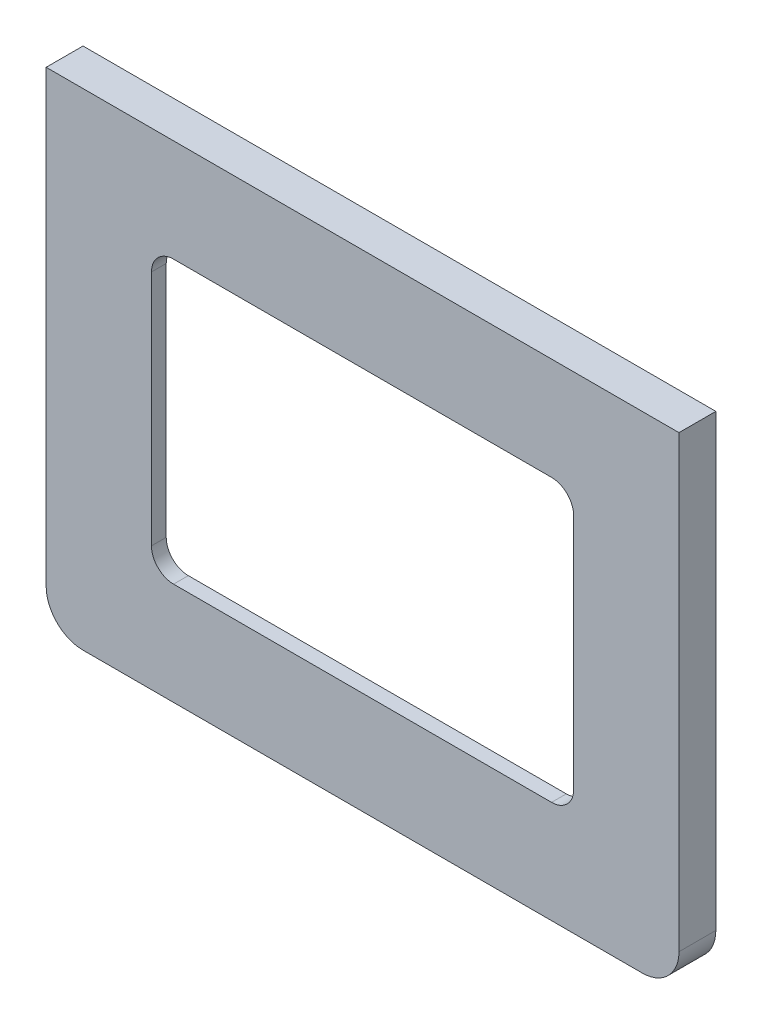
SolidWorks part; units mm, degrees
material "1023 Carbon Steel Sheet (SS)"
ref_plane "Front Plane" through (0, 0, 0) normal (0, 0, 1) x (1, 0, 0)
ref_plane "Top Plane" through (0, 0, 0) normal (0, 1, 0) x (1, 0, 0)
ref_plane "Right Plane" through (0, 0, 0) normal (1, 0, 0) x (0, 0, -1)
sketch "Sketch1" plane through (0, 0, 0) normal (0, 0, 1) x (1, 0, 0)
  line L0 (0, 30) -> (79.87, 30) construction
  line L1 (0, 0) -> (79.87, 0)
  line L2 (0, 0) -> (0, 60)
  line L3 (0, 60) -> (79.87, 60)
  line L4 (79.87, 0) -> (79.87, 60)
  line L5 (11.29, 10.905) -> (68.58, 10.905)
  line L6 (11.29, 10.905) -> (11.29, 49.095)
  line L7 (11.29, 49.095) -> (68.58, 49.095)
  line L8 (68.58, 10.905) -> (68.58, 49.095)
  line L9 (-3, 63) -> (82.87, 63)
  line L10 (82.87, -3) -> (82.87, 63)
  line L11 (-3, -3) -> (82.87, -3)
  line L12 (-3, -3) -> (-3, 63)
  dimension "D1" = 60
  dimension "D2" = 57.29
  dimension "D3" = 38.19
  dimension "D4" = 19.095
  dimension "D5" = 11.29
  dimension "D6" = 11.29
  dimension "D7" = 3
extrude "Boss-Extrude2" add sketch "Sketch1" along normal blind 5 contours L12 L11 L10 L9 L4 L1 L2 L3 | L2 L0 L6 L7 L8 L4 L3 | L0 L2 L1 L4 L8 L5 L6 | L0 L6 L5 L8 | L6 L0 L8 L7
fillet "Fillet1" radius 5 2 edges at (82.87, -3, 2.5) (-3, -3, 2.5)
sketch "Sketch4" plane through (0, 0, 0) normal (0, 0, -1) x (-1, 0, 0)
  line L8 (-80.87, 61) -> (-80.87, 2)
  line L9 (-77.87, -1) -> (-2, -1)
  line L10 (1, 2) -> (1, 61)
  line L11 (1, 61) -> (-80.87, 61)
  line L12 (-80.87, 61) -> (-80.87, 2)
  line L13 (-77.87, -1) -> (-2, -1)
  line L14 (1, 2) -> (1, 61)
  line L15 (1, 61) -> (-80.87, 61)
  arc A2 (-80.87, 2) -> (-77.87, -1) centre (-77.87, 2) ccw
  arc A3 (-80.87, 2) -> (-77.87, -1) centre (-77.87, 2) ccw
  arc A4 (-2, -1) -> (1, 2) centre (-2, 2) ccw
  arc A5 (-2, -1) -> (1, 2) centre (-2, 2) ccw
  dimension "D1" = 2
extrude "Cut-Extrude2" cut sketch "Sketch4" against normal blind 3
sketch "Sketch2" plane through (0, 0, 5) normal (0, 0, 1) x (1, 0, 0)
  line L0 (39.935, 30) -> (82.87, 30) construction
  line L1 (11.29, 49.095) -> (68.58, 49.095)
  line L2 (11.29, 49.095) -> (11.29, 10.905)
  line L3 (11.29, 10.905) -> (68.58, 10.905)
  line L4 (68.58, 49.095) -> (68.58, 10.905)
  line L7 (11.29, 30) -> (68.58, 30) construction
  line L8 (39.935, 49.095) -> (39.935, 10.905) construction
  line L9 (39.935, 63) -> (39.935, -3) construction
  line L10 (-3, 63) -> (82.87, 63) construction
  line L11 (2, -3) -> (77.87, -3) construction
  line L12 (82.87, 2) -> (82.87, 63) construction
  dimension "D1" = 57.29
  dimension "D2" = 38.19
extrude "Cut-Extrude1" cut sketch "Sketch2" against normal up to next
fillet "Fillet2" radius 3 4 edges at (68.58, 49.095, 4) (68.58, 10.905, 4) (11.29, 10.905, 4) (11.29, 49.095, 4)
sketch "Sketch3" plane through (0, 0, 3) normal (0, 0, -1) x (-1, 0, 0)
  line L1 (-68.58, 30) -> (-11.29, 30) construction
  line L2 (-11.29, 46.095) -> (-11.29, 13.905) construction
  line L4 (-68.58, 13.905) -> (-68.58, 46.095) construction
  circle A0 centre (-4, 4) radius 1.5
  circle A1 centre (-4, 56) radius 1.5
  circle A2 centre (-70.3, 56) radius 1.5
  circle A3 centre (-70.3, 4) radius 1.5
  dimension "D1" = 3
  dimension "D2" = 3
  dimension "D3" = 3
  dimension "D4" = 3
  dimension "D5" = 66.3
  dimension "D6" = 52
  dimension "D7" = 7.29
  dimension "D8" = 26
extrude "Boss-Extrude3" add sketch "Sketch3" along normal up to surface (3 mm away) up to face at (39.935, 20.4596, 0)
